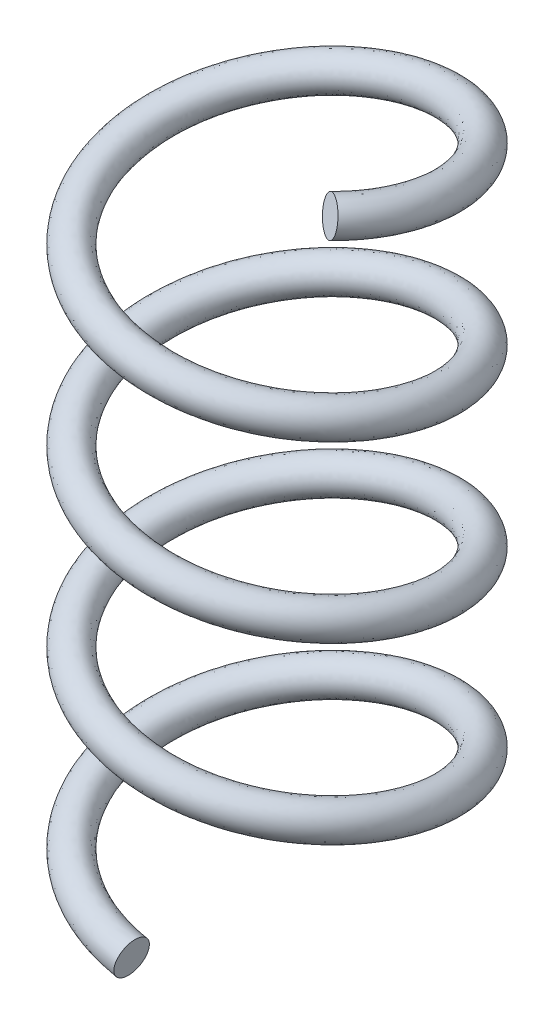
SolidWorks part; units mm, degrees
ref_plane "Plan de face" through (0, 0, 0) normal (0, 0, 1) x (1, 0, 0)
ref_plane "Plan de dessus" through (0, 0, 0) normal (0, 1, 0) x (1, 0, 0)
ref_plane "Plan de droite" through (0, 0, 0) normal (1, 0, 0) x (0, 0, -1)
sketch "Esquisse1" plane through (0, 0, 0) normal (0, 1, 0) x (1, 0, 0)
  circle A0 centre (0, 0) radius 5
  dimension "D1" = 10
curve "Hélice/Spirale1" pitch 6 height 23 turns 3.8333
sweep "Balayage1" add path "Hélice/Spirale1" circular profile diameter 1.2 parameters "D3"=1.2
